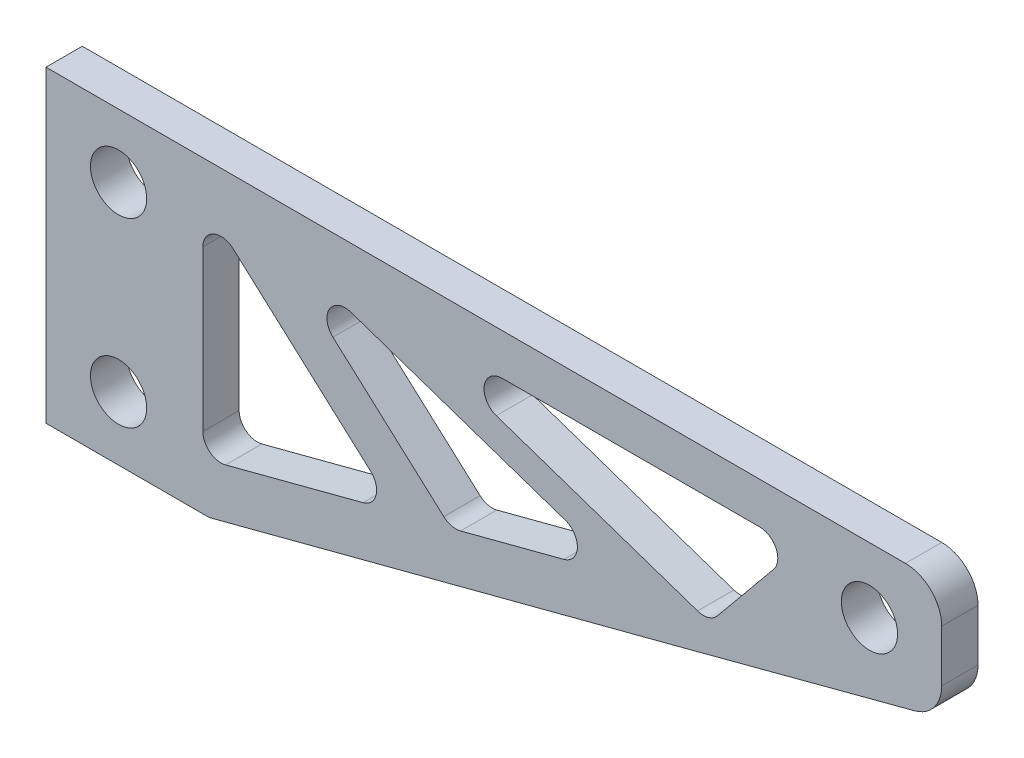
SolidWorks part; units mm, degrees
material "Thornel Mat VMA"
ref_plane "前视基准面" through (0, 0, 0) normal (0, 0, 1) x (1, 0, 0)
ref_plane "上视基准面" through (0, 0, 0) normal (0, 1, 0) x (1, 0, 0)
ref_plane "右视基准面" through (0, 0, 0) normal (1, 0, 0) x (0, 0, -1)
sketch "草图1" plane through (0, 0, 0) normal (0, 0, 1) x (1, 0, 0)
  line L0 (-13.685, 0) -> (15.4785, 0) construction
  line L1 (-4.5, 10) -> (4.5, 10)
  line L2 (-4.5, 10) -> (-4.5, -7)
  line L5 (-4.5, 10) -> (4.5, -10) construction
  line L6 (-4.5, -10) -> (4.5, 10) construction
  line L8 (15.4785, 0) -> (93.3173, 0) construction
  line L17 (4.5, 10) -> (42.8742, 10)
  line L20 (44.8742, 8) -> (44.8742, 5.1497)
  line L22 (-4.5, -7) -> (4.5, -7)
  line L23 (31.2128, 0) -> (43.385, 3.216)
  line L24 (4.5, -7) -> (31.2128, 0)
  line L32 (4.1465, 5.7451) -> (4.1465, -3.0697)
  line L34 (5.4, -4.037) -> (12.9777, -2.0513)
  line L35 (13.3937, -0.3411) -> (5.816, 6.4879)
  line L36 (11.3156, 5.0172) -> (17.4274, -0.4908)
  line L37 (18.3503, -0.7152) -> (24.0457, 0.7772)
  line L38 (24.1142, 2.6913) -> (12.3071, 6.7067)
  line L39 (20.3216, 5.7736) -> (31.4175, 2)
  line L40 (32.5123, 2.3121) -> (35.6112, 6.0857)
  line L41 (34.8384, 7.7203) -> (20.6436, 7.7203)
  circle A2 centre (-0.5, 6.5) radius 1.55
  circle A4 centre (40.8906, 6.4113) radius 1.55
  circle A5 centre (-0.5, -3.5) radius 1.55
  arc A6 (44.8742, 5.1497) -> (43.385, 3.216) centre (42.8742, 5.1497) cw
  arc A7 (44.8742, 8) -> (42.8742, 10) centre (42.8742, 8) ccw
  arc A8 (31.4175, 2) -> (32.5123, 2.3121) centre (31.7395, 2.9468) ccw
  arc A9 (35.6112, 6.0857) -> (34.8384, 7.7203) centre (34.8384, 6.7203) ccw
  arc A10 (20.6436, 7.7203) -> (20.3216, 5.7736) centre (20.6436, 6.7203) ccw
  arc A11 (17.4274, -0.4908) -> (18.3503, -0.7152) centre (18.0968, 0.2521) ccw
  arc A12 (24.0457, 0.7772) -> (24.1142, 2.6913) centre (23.7922, 1.7446) ccw
  arc A13 (12.3071, 6.7067) -> (11.3156, 5.0172) centre (11.9851, 5.76) ccw
  arc A14 (12.9777, -2.0513) -> (13.3937, -0.3411) centre (12.7242, -1.084) ccw
  arc A15 (5.816, 6.4879) -> (4.1465, 5.7451) centre (5.1465, 5.7451) ccw
  arc A16 (4.1465, -3.0697) -> (5.4, -4.037) centre (5.1465, -3.0697) ccw
  point P1 (0, 0)
  point P18 (57.0031, 0)
  dimension "D3" = 10
  dimension "D4" = 2
  dimension "D5" = 3.1
  dimension "D6" = 1
  dimension "D1" = 3.5
  dimension "D2" = 9
  dimension "D7" = 17
  dimension "D8" = 4
  dimension "D9" = 4
extrude "凸台-拉伸1" add sketch "草图1" along normal blind 2
